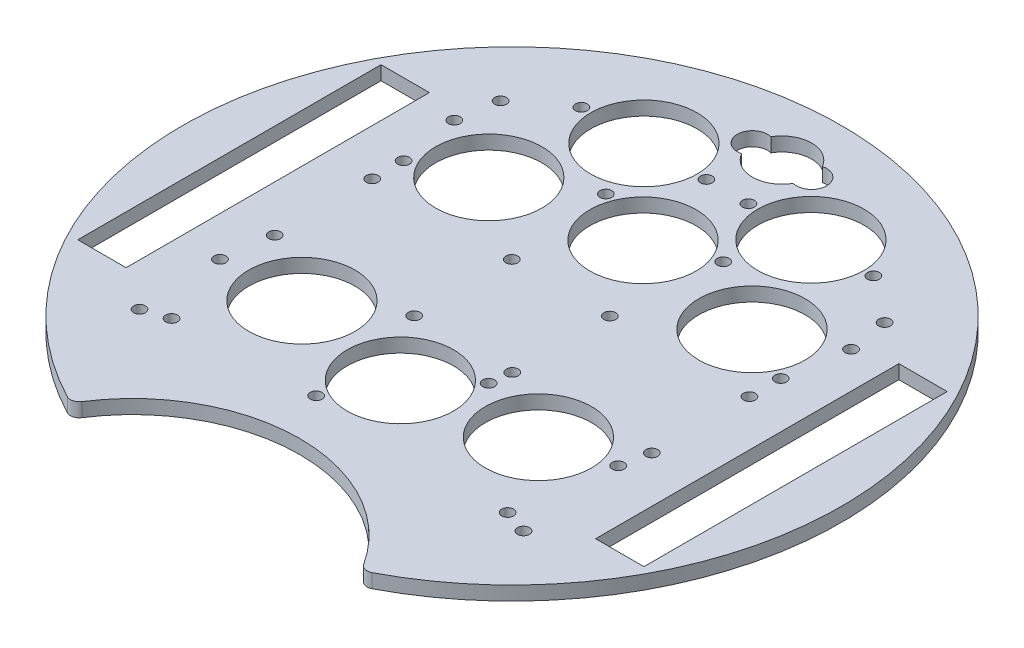
SolidWorks part; units mm, degrees
ref_plane "Front Plane" through (0, 0, 0) normal (0, 0, 1) x (1, 0, 0)
ref_plane "Top Plane" through (0, 0, 0) normal (0, 1, 0) x (1, 0, 0)
ref_plane "Right Plane" through (0, 0, 0) normal (1, 0, 0) x (0, 0, -1)
sketch "Sketch1" plane through (0, 0, 0) normal (0, 1, 0) x (1, 0, 0)
  line L1 (0, 86.2583) -> (0, -96.8543) construction
  line L2 (-50.7032, 47.6775) -> (0, 0) construction
  line L3 (-32.9956, -67.352) -> (0, -86.402) construction
  line L4 (32.9956, -67.352) -> (0, -86.402) construction
  line L5 (0, 0) -> (-13.6167, -50.8184) construction
  line L6 (55.5325, -36.9707) -> (45.152, -29.4289) construction
  line L7 (0, 0) -> (-48.2447, 57.4234) construction
  line L8 (-83.3992, 0) -> (107.0959, 0) construction
  line L9 (53.4101, -34.3971) -> (53.4101, 34.6029)
  line L10 (-64.4101, -34.3971) -> (-53.4101, -34.3971)
  line L11 (-64.4101, -34.3971) -> (-64.4101, 34.6029)
  line L12 (-64.4101, 34.6029) -> (-53.4101, 34.6029)
  line L13 (-53.4101, -34.3971) -> (-53.4101, 34.6029)
  line L14 (64.4101, 34.6029) -> (53.4101, 34.6029)
  line L15 (64.4101, -34.3971) -> (64.4101, 34.6029)
  line L16 (64.4101, -34.3971) -> (53.4101, -34.3971)
  line L17 (0, 0) -> (13.6167, -50.8184) construction
  line L18 (41.9192, -33.8784) -> (45.152, -29.4289) construction
  line L19 (0, 0) -> (48.2447, 57.4234) construction
  line L20 (52.2843, -41.4268) -> (41.9192, -33.8784) construction
  line L21 (64.9519, -37.5) -> (0, 0) construction
  line L22 (28.5723, -45.8735) -> (34.7503, -57.019) construction
  line L23 (28.5723, -45.8735) -> (23.7619, -48.54) construction
  line L24 (46.5654, 51.1495) -> (36.8089, 39.5367) construction
  line L25 (32.5978, 43.0747) -> (36.8089, 39.5367) construction
  line L26 (23.7619, -48.54) -> (29.9399, -59.6854) construction
  line L27 (-28.5723, -45.8735) -> (-34.7503, -57.019) construction
  line L28 (-23.7619, -48.54) -> (-29.9399, -59.6854) construction
  line L29 (-18.4555, -45.8919) -> (-23.0541, -33.9225) construction
  line L30 (-23.0541, -33.9225) -> (-17.92, -31.9499) construction
  line L31 (-28.5723, -45.8735) -> (-23.7619, -48.54) construction
  line L32 (-42.3565, 54.69) -> (-32.5978, 43.0747) construction
  line L33 (-32.5978, 43.0747) -> (-36.8089, 39.5367) construction
  line L34 (42.3565, 54.69) -> (32.5978, 43.0747) construction
  line L35 (-13.6167, -50.8184) -> (-25.1096, -20.9046) construction
  line L36 (-46.5654, 51.1495) -> (-36.8089, 39.5367) construction
  line L37 (-13.3214, -43.9193) -> (-17.92, -31.9499) construction
  line L38 (13.6167, -50.8184) -> (24.3327, -22.8079) construction
  line L39 (18.4555, -45.8919) -> (23.0541, -33.9225) construction
  line L40 (23.0541, -33.9225) -> (17.92, -31.9499) construction
  line L41 (13.3214, -43.9193) -> (17.92, -31.9499) construction
  line L42 (-58.5537, 0) -> (91.2411, 0) construction
  line L43 (-55.5325, -36.9707) -> (-45.152, -29.4289) construction
  line L44 (-52.2843, -41.4268) -> (-41.9192, -33.8784) construction
  line L45 (-41.9192, -33.8784) -> (-45.152, -29.4289) construction
  line L46 (0, 34.6626) -> (0, -51.647) construction
  line L47 (-37.1849, 0) -> (48.113, 0) construction
  line L48 (0, 49.2959) -> (0, -33.0158) construction
  line L54 (8.45, 45.0502) -> (-8.45, 71.1502) construction
  line L55 (8.45, 71.1502) -> (-8.45, 45.0502) construction
  arc A0 (32.9956, -67.352) -> (-32.9956, -67.352) centre (0, 0) ccw
  arc A1 (32.9956, -67.352) -> (-32.9956, -67.352) centre (0, -86.402) ccw
  circle A2 centre (0, 0) radius 74 construction
  arc A3 (54.6382, 51.3777) -> (46.5385, 51.1172) centre (50.7032, 47.6775) ccw construction
  arc A4 (-54.6382, 51.3777) -> (-46.5385, 51.1172) centre (-50.7032, 47.6775) cw construction
  arc A5 (-45.9, -59.3143) -> (-34.7503, -57.019) centre (-41.31, -53.3829) ccw construction
  arc A6 (45.9, -59.3143) -> (34.7503, -57.019) centre (41.31, -53.3829) cw construction
  arc A7 (-41.1872, 62.6787) -> (-42.3272, 54.6554) centre (-38.2209, 58.1646) ccw construction
  arc A8 (-25.9781, -70.3572) -> (-29.9399, -59.6854) centre (-23.3803, -63.3215) cw construction
  arc A9 (25.9781, -70.3572) -> (29.9399, -59.6854) centre (23.3803, -63.3215) ccw construction
  arc A10 (41.1872, 62.6787) -> (42.3272, 54.6554) centre (38.2209, 58.1646) cw construction
  arc A11 (53.2525, -52.8127) -> (52.2843, -41.4268) centre (47.9272, -47.5314) ccw construction
  arc A12 (66.658, -34.376) -> (55.5325, -36.9707) centre (59.9914, -30.9401) cw construction
  arc A13 (-5.2684, -48.6449) -> (-13.3214, -43.9193) centre (-6.3241, -41.2196) cw construction
  arc A14 (-21.2728, -54.7938) -> (-18.4555, -45.8919) centre (-25.4604, -48.5717) ccw construction
  arc A15 (-66.658, -34.376) -> (-55.5325, -36.9707) centre (-59.9914, -30.9401) ccw construction
  arc A16 (-53.2525, -52.8127) -> (-52.2843, -41.4268) centre (-47.9272, -47.5314) cw construction
  arc A17 (21.2728, -54.7938) -> (18.4555, -45.8919) centre (25.4604, -48.5717) cw construction
  arc A18 (5.2684, -48.6449) -> (13.3214, -43.9193) centre (6.3241, -41.2196) ccw construction
  circle A19 centre (-42.9101, 11.1) radius 1.35
  circle A20 centre (-42.9101, -11.1) radius 1.35
  circle A21 centre (-11.1601, -11.1) radius 1.35
  circle A22 centre (-11.1601, 11.1) radius 1.35
  circle A23 centre (11.1601, 11.1) radius 1.35
  circle A24 centre (11.1601, -11.1) radius 1.35
  circle A25 centre (42.9101, -11.1) radius 1.35
  circle A26 centre (42.9101, 11.1) radius 1.35
  circle A27 centre (26.9058, -20.9046) radius 12.095
  circle A28 centre (19, 49) radius 12.095
  circle A29 centre (0, 29.7936) radius 12.095
  circle A30 centre (0, -25.4092) radius 12.095
  circle A31 centre (29.9399, 24.6519) radius 12.095
  circle A32 centre (-26.9058, -20.9046) radius 12.095
  circle A33 centre (6.731, 61.4226) radius 1.143
  circle A34 centre (-6.731, 61.4226) radius 1.143
  arc A35 (-5.8539, 64.7449) -> (5.8576, 64.7385) centre (0, 61.4226) cw
  arc A36 (5.8576, 64.7385) -> (5.8576, 58.1067) centre (6.731, 61.4226) cw
  arc A37 (-5.8539, 58.1002) -> (-5.8539, 64.7449) centre (-6.731, 61.4226) cw
  arc A38 (5.8576, 58.1067) -> (-5.8539, 58.1002) centre (0, 61.4226) cw
  circle A39 centre (-29.9399, 24.6519) radius 12.095
  circle A40 centre (-33.218, 49) radius 1.35
  circle A41 centre (-4.782, 49) radius 1.35
  circle A42 centre (4.782, 49) radius 1.35
  circle A43 centre (-31.7919, 27.0969) radius 12.095 construction
  circle A44 centre (-42.9101, 18.2348) radius 1.35
  circle A45 centre (42.9101, 18.2348) radius 1.35
  circle A46 centre (-31.0383, -26.9744) radius 12.095 construction
  circle A47 centre (31.0383, -26.9744) radius 12.095 construction
  circle A48 centre (31.7919, 27.0969) radius 12.095 construction
  circle A49 centre (-19, 49) radius 12.095
  circle A50 centre (45.1387, 31.9972) radius 1.35
  circle A51 centre (-45.1387, 31.9972) radius 1.35
  circle A52 centre (13.3469, 34.6938) radius 1.35
  circle A53 centre (-6.5548, -38.0261) radius 1.35
  circle A54 centre (-31.7919, 27.0969) radius 14.218 construction
  circle A55 centre (-13.3469, 34.6938) radius 1.35
  circle A56 centre (10.597, -15.93) radius 1.35
  circle A57 centre (-38.2343, -39.237) radius 1.35
  circle A58 centre (0, 29.7936) radius 14.218 construction
  circle A59 centre (-43.6846, -41.0778) radius 1.35
  circle A60 centre (-43.6846, 41.0778) radius 1.35
  circle A61 centre (43.6846, -41.0778) radius 1.35
  circle A62 centre (31.7919, 27.0969) radius 14.218 construction
  circle A63 centre (33.218, 49) radius 1.35
  circle A64 centre (0, 0) radius 59.9644 construction
  circle A66 centre (-19, 49) radius 14.218 construction
  circle A67 centre (43.6846, 41.0778) radius 1.35
  circle A70 centre (19, 49) radius 14.218 construction
  circle A71 centre (-44.3852, -22.0742) radius 1.35
  circle A74 centre (-31.0383, -26.9744) radius 14.218 construction
  circle A78 centre (0, -25.4092) radius 14.218 construction
  circle A80 centre (41.6017, -17.4578) radius 1.35
  circle A81 centre (38.2343, -39.237) radius 1.35
  circle A82 centre (31.0383, -26.9744) radius 14.218 construction
  point P14 (-62.6039, 0)
  point P23 (62.6039, 0)
  point P35 (-31.5178, -45.012)
  point P40 (-46.7211, -26.9744)
  point P45 (-34.7033, 41.3057)
  point P84 (-20.4871, -32.9362)
  point P154 (0, 58.1002)
  dimension "D1" = 150
  dimension "D2" = 76.2
  dimension "D10" = 148
  dimension "D13" = 2.7
  dimension "D14" = 2.7
  dimension "D22" = 2.286
  dimension "D20" = 2.7
  dimension "D27" = 2.7
  dimension "D28" = 2.7
  dimension "D3" = 120
  dimension "D4" = 69
  dimension "D5" = 11
  dimension "D9" = 30
  dimension "D16" = 5.5
  dimension "D7" = 5.5
  dimension "D8" = 12.8224
  dimension "D6" = 12.8224
  dimension "D11" = 5.5
  dimension "D12" = 5.5
  dimension "D17" = 22.2
  dimension "D19" = 22.2
  dimension "D15" = 10.5
  dimension "D18" = 31.75
  dimension "D23" = 13.462
  dimension "D24" = 16.9
  dimension "D25" = 26.1
  dimension "D21" = 38
  dimension "D26" = 49
  dimension "D29" = 6.726
extrude "Boss-Extrude2" add sketch "Sketch1" along normal blind 3.175
fillet "Fillet1" radius 2 2 edges at (-32.9956, 1.5875, 67.352) (32.9956, 1.5875, 67.352)
equation "\"D10@Sketch1\"=150-2"
